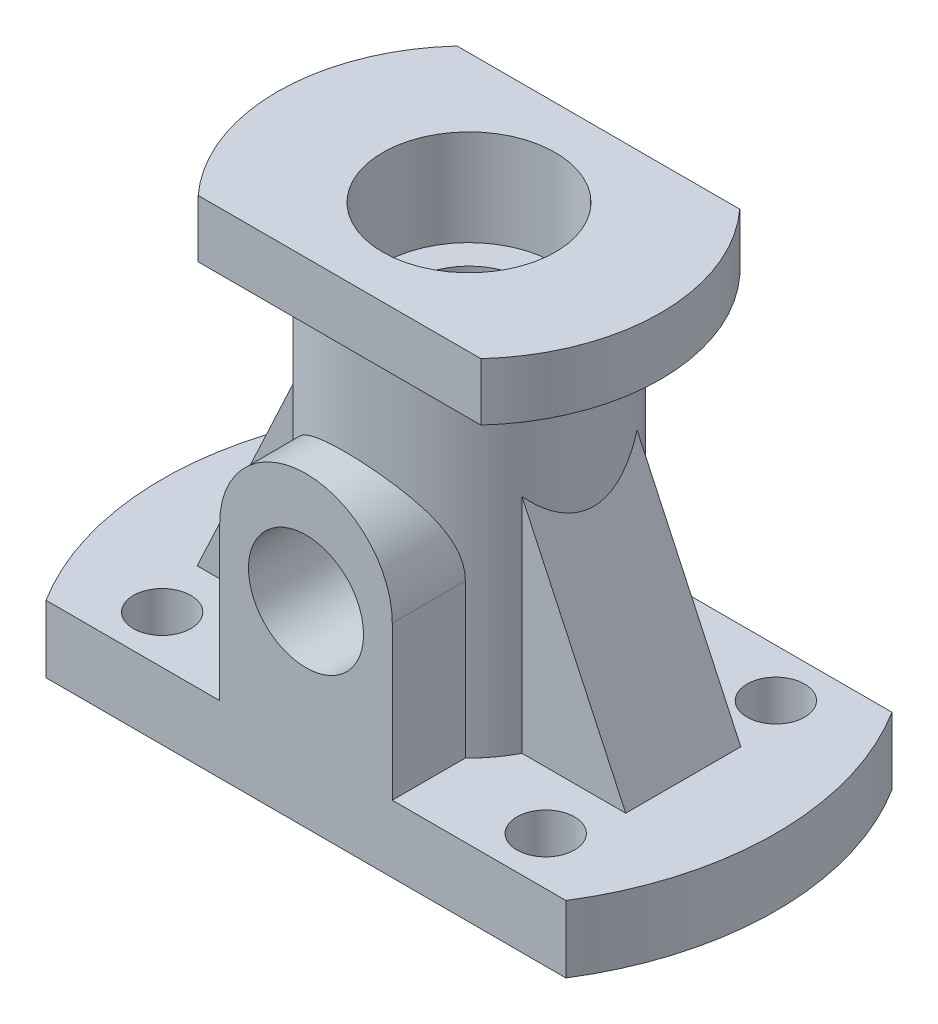
SolidWorks part; units mm, degrees
ref_plane "前视基准面" through (0, 0, 0) normal (0, 0, 1) x (1, 0, 0)
ref_plane "上视基准面" through (0, 0, 0) normal (0, 1, 0) x (1, 0, 0)
ref_plane "右视基准面" through (0, 0, 0) normal (1, 0, 0) x (0, 0, -1)
sketch "草图1" plane through (0, 0, 0) normal (0, 1, 0) x (1, 0, 0)
  line L0 (-27.1109, 17) -> (27.1109, 17)
  line L1 (0, 0) -> (48.9662, 0) construction
  line L3 (-27.1109, -17) -> (27.1109, -17)
  arc A0 (-27.1109, 17) -> (-27.1109, -17) centre (0, 0) ccw
  arc A1 (27.1109, -17) -> (27.1109, 17) centre (0, 0) ccw
  dimension "D1" = 64
  dimension "D2" = 17
extrude "凸台-拉伸1" add sketch "草图1" along normal blind 7
sketch "草图2" plane through (0, 7, 0) normal (0, 1, 0) x (1, 0, 0)
  circle A0 centre (-20, -12) radius 3
  dimension "D1" = 6
  dimension "D2" = 20
  dimension "D3" = 12
extrude "切除-拉伸1" cut sketch "草图2" against normal through all
mirror "镜向1" about plane through (0, 0, 0) normal (1, 0, 0) of "切除-拉伸1"
mirror "镜向2" about plane through (0, 0, 0) normal (0, 0, 1) of "镜向1", "切除-拉伸1"
sketch "草图3" plane through (0, 7, 0) normal (0, 1, 0) x (1, 0, 0)
  circle A0 centre (0, 0) radius 13
  dimension "D1" = 26
extrude "凸台-拉伸2" add sketch "草图3" along normal blind 35
sketch "草图4" plane through (0, 42, 0) normal (0, 1, 0) x (1, 0, 0)
  line L0 (-14.7369, 13.5) -> (14.7369, 13.5)
  line L1 (0, 0) -> (21.0258, 0) construction
  line L2 (-14.7369, -13.5) -> (14.7369, -13.5)
  arc A0 (-14.7369, 13.5) -> (-14.7369, -13.5) centre (0, 0) ccw
  arc A1 (14.7369, -13.5) -> (14.7369, 13.5) centre (0, 0) ccw
  dimension "D1" = 13.5
extrude "凸台-拉伸3" add sketch "草图4" along normal blind 6
sketch "草图5" plane through (0, 48, 0) normal (0, 1, 0) x (1, 0, 0)
  circle A0 centre (0, 0) radius 9
  dimension "D1" = 18
extrude "切除-拉伸2" cut sketch "草图5" against normal blind 10
sketch "草图6" plane through (0, 38, 0) normal (0, 1, 0) x (1, 0, 0)
  circle A0 centre (0, 0) radius 6
  dimension "D1" = 12
extrude "切除-拉伸3" cut sketch "草图6" against normal through all
sketch "草图7" plane through (0, 0, 17) normal (0, 0, 1) x (1, 0, 0)
  line L0 (-9, 7) -> (-9, 23)
  line L1 (-27.1109, 7) -> (27.1109, 7) construction
  line L3 (9, 23) -> (9, 7)
  line L4 (9, 7) -> (-9, 7)
  line L5 (-27.1109, 0) -> (27.1109, 0) construction
  arc A0 (9, 23) -> (-9, 23) centre (0, 23) ccw
  dimension "D1" = 9
  dimension "D2" = 9
  dimension "D3" = 23
extrude "凸台-拉伸4" add sketch "草图7" against normal up to surface (7.6192 mm away)
sketch "草图8" plane through (0, 0, 17) normal (0, 0, 1) x (1, 0, 0)
  circle A0 centre (0, 20.4617) radius 6
  dimension "D1" = 12
extrude "切除-拉伸4" cut sketch "草图8" against normal up to next
sketch "草图10" plane through (0, 0, 0) normal (0, 0, 1) x (1, 0, 0)
  line L0 (-10.4933, 6.9457) -> (-22.3438, 7)
  line L1 (-27.1109, 7) -> (-9, 7) construction
  line L3 (-22.3438, 7) -> (-14.9415, 22.8742)
  line L4 (-14.9415, 22.8742) -> (-10.6661, 32.043)
  line L5 (-10.6661, 32.043) -> (-10.4933, 6.9457)
extrude "凸台-拉伸6" add sketch "草图10" along normal blind 6 and the other way blind 6 from surface at 0 contours L5 L0 L3 L4 starting at plane "前视基准面"
mirror "镜向4" about plane through (0, 0, 0) normal (1, 0, 0) of "凸台-拉伸6"
